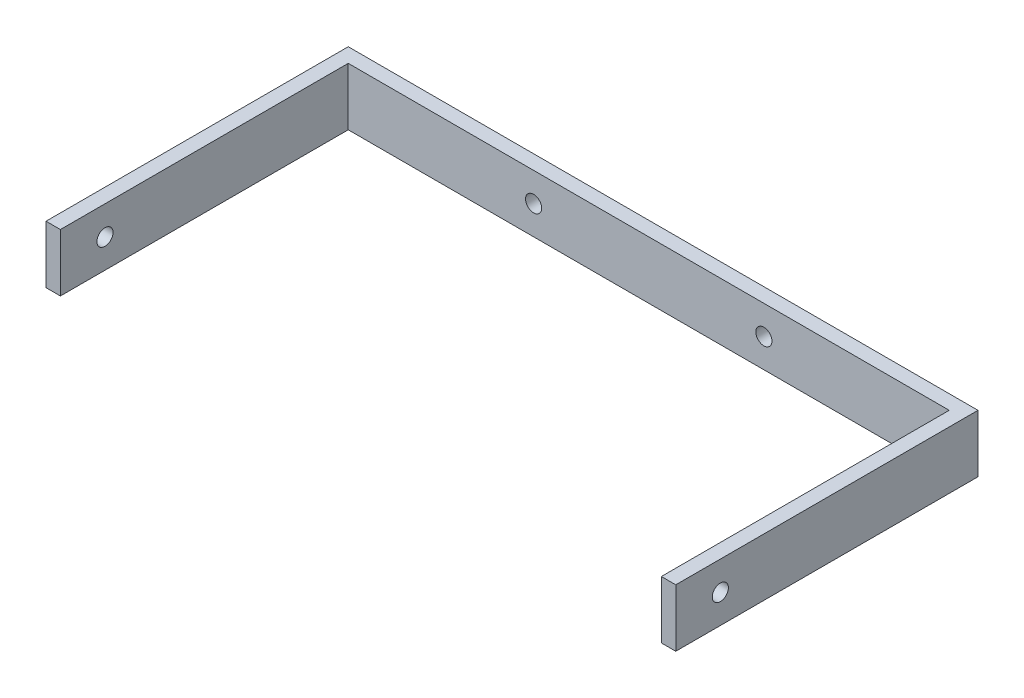
SolidWorks part; units mm, degrees
material "Copper"
ref_plane "Front Plane" through (0, 0, 0) normal (0, 0, 1) x (1, 0, 0)
ref_plane "Top Plane" through (0, 0, 0) normal (0, 1, 0) x (1, 0, 0)
ref_plane "Right Plane" through (0, 0, 0) normal (1, 0, 0) x (0, 0, -1)
sketch "Sketch1" plane through (0, 0, 0) normal (0, 0, 1) x (1, 0, 0)
  line L1 (0, 0) -> (-138.9256, 0)
  line L2 (0, 0) -> (0, -12.7)
  line L3 (0, -12.7) -> (-138.9256, -12.7)
  line L4 (-138.9256, 0) -> (-138.9256, -12.7)
  circle A0 centre (-94.8628, -6.35) radius 1.778
  circle A1 centre (-44.0628, -6.35) radius 1.778
  point P9 (-69.4628, 0)
  dimension "D3" = 3.556
  dimension "D4" = 3.556
  dimension "D5" = 6.35
  dimension "D1" = 138.9256
  dimension "D2" = 12.7
  dimension "D6" = 6.35
  dimension "D7" = 50.8
  dimension "D8" = 25.4
extrude "Boss-Extrude1" add sketch "Sketch1" along normal blind 3.175
sketch "Sketch2" plane through (0, 0, 3.175) normal (0, 0, 1) x (1, 0, 0)
  line L0 (-138.9256, -12.7) -> (0, -12.7) construction
  line L1 (-138.9256, 0) -> (-135.7506, 0)
  line L2 (-138.9256, 0) -> (-138.9256, -12.7)
  line L3 (-138.9256, -12.7) -> (-135.7506, -12.7)
  line L4 (-135.7506, 0) -> (-135.7506, -12.7)
  line L6 (0, 0) -> (-3.175, 0)
  line L7 (0, 0) -> (0, -12.7)
  line L8 (0, -12.7) -> (-3.175, -12.7)
  line L9 (-3.175, 0) -> (-3.175, -12.7)
  dimension "D1" = 3.175
  dimension "D2" = 3.175
extrude "Boss-Extrude2" add sketch "Sketch2" along normal blind 63.5
sketch "Sketch3" plane through (0, 0, 0) normal (1, 0, 0) x (0, 0, -1)
  line L0 (-66.675, 0) -> (0, 0) construction
  line L1 (0, -12.7) -> (0, 0) construction
  circle A0 centre (-56.8402, -6.35) radius 1.778
  dimension "D1" = 3.556
  dimension "D2" = 6.35
  dimension "D3" = 56.8402
extrude "Cut-Extrude1" cut sketch "Sketch3" against normal blind 152.4
